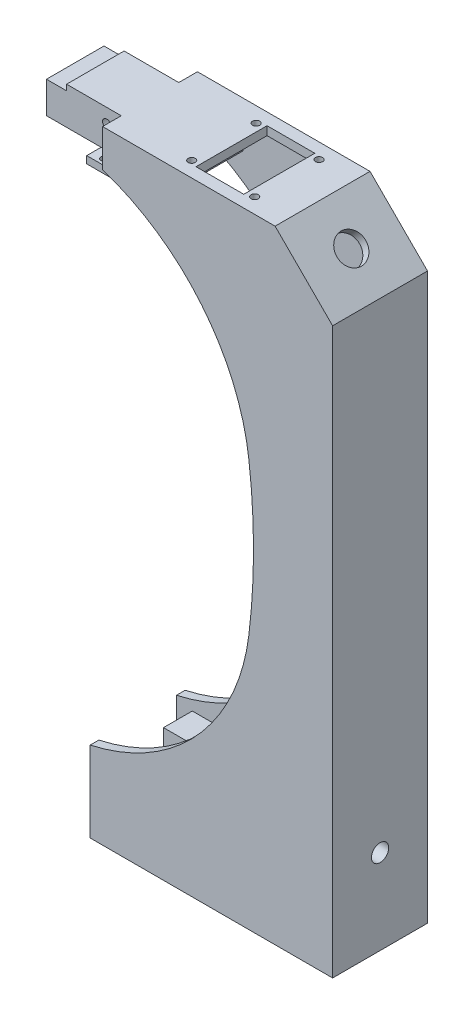
SolidWorks part; units mm, degrees
ref_plane "Спереди" through (0, 0, 0) normal (0, 0, 1) x (1, 0, 0)
ref_plane "Сверху" through (0, 0, 0) normal (0, 1, 0) x (1, 0, 0)
ref_plane "Справа" through (0, 0, 0) normal (1, 0, 0) x (0, 0, -1)
other "Configuration Table"
sketch "Эскиз1" plane through (0, 0, 0) normal (0, 0, 1) x (1, 0, 0)
  line L1 (4.2996, 175.4028) -> (4.2996, 188.4028)
  line L4 (84.2996, 0) -> (84.2996, 168.4028)
  line L7 (64.2996, 188.4028) -> (4.2996, 188.4028)
  line L11 (0, 0) -> (0, -28)
  line L12 (84.2996, 0) -> (84.2996, -28)
  line L13 (84.2996, -28) -> (0, -28)
  line L14 (64.2996, 188.4028) -> (84.2996, 168.4028)
  arc A0 (0, 0) -> (55.1731, 60.6624) centre (-15.2954, 69.3329) ccw
  arc A1 (55.1731, 113.6624) -> (4.2996, 175.4028) centre (-18.7693, 104.5645) ccw
  arc A2 (55.1731, 60.6624) -> (55.1731, 113.6624) centre (-160.2027, 87.1624) ccw
  dimension "D1" = 142
  dimension "D3" = 149
  dimension "D5" = 53
  dimension "D6" = 217
  dimension "D2" = 82
  dimension "D4" = 80
  dimension "D7" = 125.5129
  dimension "D8" = 126.3456
  dimension "D9" = 15.2954
  dimension "D10" = 69.3329
  dimension "D11" = 160.2027
  dimension "D12" = 87.1624
  dimension "D13" = 104.5645
  dimension "D14" = 18.7693
  dimension "D15" = 4.2996
  dimension "D16" = 175.4028
  dimension "D17" = 80
  dimension "D18" = 168.4028
  dimension "D19" = 60
  dimension "D20" = 28
  dimension "D21" = 84.2996
  dimension "D22" = 28
  dimension "D23" = 20
  dimension "D24" = 216.4028
extrude "Бобышка-Вытянуть6" add sketch "Эскиз1" along normal blind 33
sketch "Эскиз5" plane through (0, 0, 0) normal (0, 0, 1) x (1, 0, 0)
  line L0 (-18.7004, -25) -> (81.2996, -25)
  line L3 (23.057, 175.4028) -> (4.2996, 175.4028)
  line L4 (-18.7004, 167.1602) -> (-18.7004, -25)
  line L5 (84.2996, -28) -> (84.2996, 168.4028) construction
  line L6 (81.2996, -25) -> (81.2996, -3.5)
  line L8 (23.057, 175.4028) -> (23.057, 185.4028)
  line L9 (23.057, 185.4028) -> (63.057, 185.4028)
  line L10 (63.057, 185.4028) -> (81.2996, 167.1602)
  line L11 (84.2996, 168.4028) -> (64.2996, 188.4028) construction
  line L12 (64.2996, 188.4028) -> (4.2996, 188.4028) construction
  line L13 (-18.7004, 167.1602) -> (6.2996, 167.1602)
  line L14 (6.2996, 167.1602) -> (4.2996, 175.4028)
  line L15 (81.2996, -3.5) -> (14, -3.5)
  line L16 (81.2996, 6.5) -> (14, 6.5)
  line L17 (14, 6.5) -> (14, -3.5)
  line L18 (0, 0) -> (0, -28) construction
  line L19 (81.2996, 167.1602) -> (81.2996, 6.5)
  dimension "D1" = 21.5
  dimension "D2" = 3
  dimension "D3" = 3
  dimension "D4" = 3
  dimension "D5" = 3
  dimension "D6" = 40
  dimension "D7" = 100
  dimension "D8" = 25
  dimension "D9" = 8.2426
  dimension "D10" = 10
  dimension "D11" = 14
  dimension "D12" = 160.6602
extrude "Вырез-Вытянуть2" cut sketch "Эскиз5" along normal blind 27 from offset 3
sketch "Эскиз7" plane through (0, 0, 0) normal (0, 0, 1) x (1, 0, 0)
  line L1 (4.2996, 188.4028) -> (-21.7004, 188.4028)
  line L2 (4.2996, 188.4028) -> (4.2996, 175.4028)
  line L3 (4.2996, 175.4028) -> (-21.7004, 175.4028)
  line L4 (-21.7004, 188.4028) -> (-21.7004, 175.4028)
  dimension "D1" = 26
extrude "Бобышка-Вытянуть7" add sketch "Эскиз7" along normal blind 20 from offset 6.5
sketch "Эскиз11" plane through (0, 0, 0) normal (0, 0, 1) x (1, 0, 0)
  line L1 (10.2996, 175.4028) -> (-2.7004, 175.4028)
  line L2 (10.2996, 175.4028) -> (10.2996, 172.9028)
  line L3 (10.2996, 172.9028) -> (-2.7004, 172.9028)
  line L4 (-2.7004, 175.4028) -> (-2.7004, 172.9028)
  dimension "D1" = 6
  dimension "D2" = 2.5
  dimension "D3" = 13
  dimension "D4" = 7
extrude "Бобышка-Вытянуть15" add sketch "Эскиз11" along normal blind 30 from offset 1.5
sketch "Эскиз12" plane through (0, 0, 0) normal (0, 1, 0) x (1, 0, 0)
  circle A0 centre (1.1427, -3.5) radius 1
  circle A1 centre (1.1427, -29.5) radius 1
  dimension "D1" = 2
  dimension "D2" = 2
  dimension "D3" = 26
  dimension "D4" = 3.5
  dimension "D5" = 1.1427
  dimension "D6" = 1.1427
extrude "Вырез-Вытянуть3" cut sketch "Эскиз12" against normal blind 10 from offset 180
sketch "Эскиз13" plane through (0, 0, 0) normal (0, 0, 1) x (1, 0, 0)
  line L0 (4.2996, 188.4028) -> (-21.7004, 188.4028) construction
  line L1 (-21.7004, 188.4028) -> (-21.7004, 175.4028) construction
  circle A0 centre (-0.7004, 183.4028) radius 1.5
  dimension "D1" = 5
  dimension "D3" = 3
  dimension "D2" = 21
extrude "Вырез-Вытянуть4" cut sketch "Эскиз13" along normal blind 30
sketch "Эскиз14" plane through (0, 0, 0) normal (0, 0, 1) x (1, 0, 0)
  line L1 (-21.7004, 188.4028) -> (-14.7004, 188.4028)
  line L2 (-21.7004, 188.4028) -> (-21.7004, 186.4028)
  line L3 (-21.7004, 186.4028) -> (-14.7004, 186.4028)
  line L4 (-14.7004, 188.4028) -> (-14.7004, 186.4028)
  dimension "D1" = 2
  dimension "D2" = 7
extrude "Вырез-Вытянуть5" cut sketch "Эскиз14" along normal blind 30
sketch "Эскиз15" plane through (0, 0, 0) normal (0, 0, 1) x (1, 0, 0)
  line L1 (81.2996, -3.5) -> (14, -3.5)
  line L2 (81.2996, -3.5) -> (81.2996, 6.5)
  line L3 (81.2996, 6.5) -> (14, 6.5)
  line L4 (14, -3.5) -> (14, 6.5)
  dimension "D1" = 67.2996
  dimension "D2" = 10
extrude "Бобышка-Вытянуть16" add sketch "Эскиз15" along normal blind 10 from offset 11.5
sketch "Эскиз16" plane through (0, 0, 0) normal (1, 0, 0) x (0, 0, -1)
  line L0 (-30, -3.5) -> (-3, -3.5) construction
  line L1 (-3, 6.5) -> (-11.5, 6.5)
  line L2 (-3, 6.5) -> (-3, -3.5)
  line L3 (-3, -3.5) -> (-11.5, -3.5)
  line L4 (-11.5, 6.5) -> (-11.5, -3.5)
  line L6 (-30, -3.5) -> (-21.5, -3.5)
  line L7 (-30, -3.5) -> (-30, 6.5)
  line L8 (-30, 6.5) -> (-21.5, 6.5)
  line L9 (-21.5, -3.5) -> (-21.5, 6.5)
  dimension "D1" = 8.5
extrude "Вырез-Вытянуть6" cut sketch "Эскиз16" along normal blind 79
sketch "Эскиз17" plane through (0, 0, 0) normal (1, 0, 0) x (0, 0, -1)
  circle A0 centre (-16.5, 1.5) radius 3
  dimension "D1" = 6
  dimension "D2" = 1.5
  dimension "D3" = 16.5
extrude "Вырез-Вытянуть7" cut sketch "Эскиз17" along normal blind 75 from offset 16.5
sketch "Эскиз18" plane through (0, 0, 0) normal (1, 0, 0) x (0, 0, -1)
  circle A0 centre (-16.5, 1.5) radius 1.5
  dimension "D1" = 3
extrude "Вырез-Вытянуть9" cut sketch "Эскиз18" along normal blind 5 from offset 13
sketch "Эскиз19" plane through (126.3512, 126.3512, 0) normal (0.7071, 0.7071, 0) x (0, 0, -1)
sketch "Эскиз20" plane through (0, 188.4028, 0) normal (0, 1, 0) x (1, 0, 0)
  line L4 (32.65, -4.15) -> (32.65, -28.85)
  line L5 (32.65, -28.85) -> (49.25, -28.85)
  line L6 (32.65, -4.15) -> (49.25, -4.15)
  line L7 (49.25, -4.15) -> (49.25, -28.85)
  line L13 (-21.7004, -26.5) -> (-21.7004, -6.5) construction
  circle A0 centre (51.9, -5.3) radius 1.25
  circle A1 centre (51.9, -27.7) radius 1.25
  circle A2 centre (30, -5.3) radius 1.25
  circle A3 centre (30, -27.7) radius 1.25
  dimension "D1" = 21.9
  dimension "D13" = 2.5
  dimension "D14" = 2.5
  dimension "D15" = 2.5
  dimension "D16" = 2.5
  dimension "D2" = 22.4
  dimension "D3" = 16.6
  dimension "D4" = 24.7
  dimension "D5" = 30
  dimension "D6" = 21.9
  dimension "D7" = 22.4
  dimension "D8" = 31.3268
  dimension "D9" = 32.65
  dimension "D10" = 4.15
  dimension "D11" = 51.9
  dimension "D12" = 27.7
  dimension "D17" = 49.25
extrude "Вырез-Вытянуть10" cut sketch "Эскиз20" against normal blind 5
sketch "Эскиз21" plane through (126.3512, 126.3512, 0) normal (0.7071, 0.7071, 0) x (0, 0, -1)
  line L0 (0, 59.47) -> (0, 87.7542) construction
  line L1 (0, 73.6121) -> (-33, 73.6121)
  line L2 (-33, 59.47) -> (-33, 87.7542) construction
  line L3 (-16.5, 87.7542) -> (-16.5, 59.47)
  line L4 (-33, 87.7542) -> (0, 87.7542) construction
  line L5 (-33, 59.47) -> (0, 59.47) construction
  circle A0 centre (-16.5, 73.6121) radius 5
  point P17 (-16.5, 73.6121)
  dimension "D1" = 10
extrude "Вырез-Вытянуть11" cut sketch "Эскиз21" against normal blind 5 contours A0
